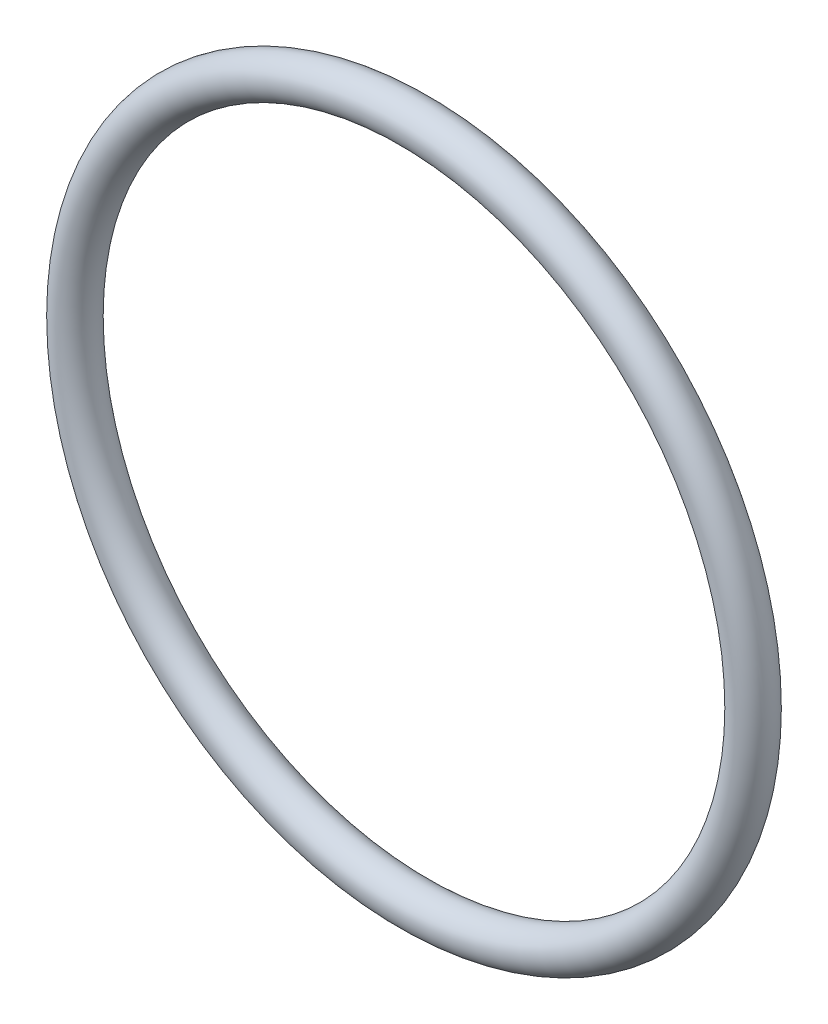
SolidWorks part; units mm, degrees
ref_plane "Front" through (0, 0, 0) normal (0, 0, 1) x (1, 0, 0)
ref_plane "Top" through (0, 0, 0) normal (0, 1, 0) x (1, 0, 0)
ref_plane "Right" through (0, 0, 0) normal (1, 0, 0) x (0, 0, -1)
sketch "Sketch1" plane through (0, 0, 0) normal (1, 0, 0) x (0, -1, 0)
  line L0 (0, -2.667) -> (0, 2.667) construction
  line L2 (-52.6669, 0) -> (52.6669, 0) construction
  line L3 (-42.545, 0) -> (42.545, 0) construction
  circle A0 centre (45.212, 0) radius 2.667
  point P9 (42.545, 0)
  point P10 (47.879, 0)
  point P13 (45.212, 2.667)
  point P14 (45.212, -2.667)
  dimension "Width" = 5.334
  dimension "ID" = 85.09
revolve "Revolve1" add sketch "Sketch1" angle 360 about L0
